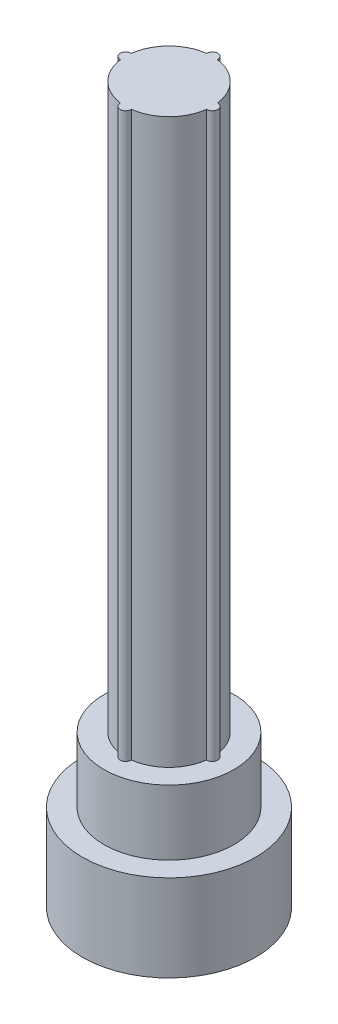
SolidWorks part; units mm, degrees
ref_plane "Front Plane" through (0, 0, 0) normal (0, 0, 1) x (1, 0, 0)
ref_plane "Top Plane" through (0, 0, 0) normal (0, 1, 0) x (1, 0, 0)
ref_plane "Right Plane" through (0, 0, 0) normal (1, 0, 0) x (0, 0, -1)
sketch "Sketch1" plane through (0, 0, 0) normal (0, 1, 0) x (1, 0, 0)
  circle A0 centre (0, 0) radius 2
  dimension "D1" = 4
extrude "Boss-Extrude1" add sketch "Sketch1" along normal blind 2
sketch "Sketch2" plane through (0, 2, 0) normal (0, 1, 0) x (1, 0, 0)
  circle A0 centre (0, 0) radius 1.5
  dimension "D1" = 3
extrude "Boss-Extrude2" add sketch "Sketch2" along normal blind 1.5
sketch "Sketch3" plane through (0, 3.5, 0) normal (0, 1, 0) x (1, 0, 0)
  circle A0 centre (0, 0) radius 1
  dimension "D1" = 2
extrude "Boss-Extrude3" add sketch "Sketch3" along normal blind 13
sketch "Sketch4" plane through (0, 16.5, 0) normal (0, 1, 0) x (1, 0, 0)
  line L0 (0, 1) -> (0, -1) construction
  line L1 (-1, 0) -> (1, 0) construction
  circle A0 centre (0, 0) radius 1 construction
  circle A1 centre (0, 0) radius 1 construction
  circle A2 centre (0, 1) radius 0.125
  circle A3 centre (-1, 0) radius 0.125
  circle A4 centre (0, -1) radius 0.125
  circle A5 centre (1, 0) radius 0.125
  dimension "D1" = 0.25
extrude "Boss-Extrude4" add sketch "Sketch4" against normal up to surface (13 mm away) up to face at (0, 3.5, 1)
